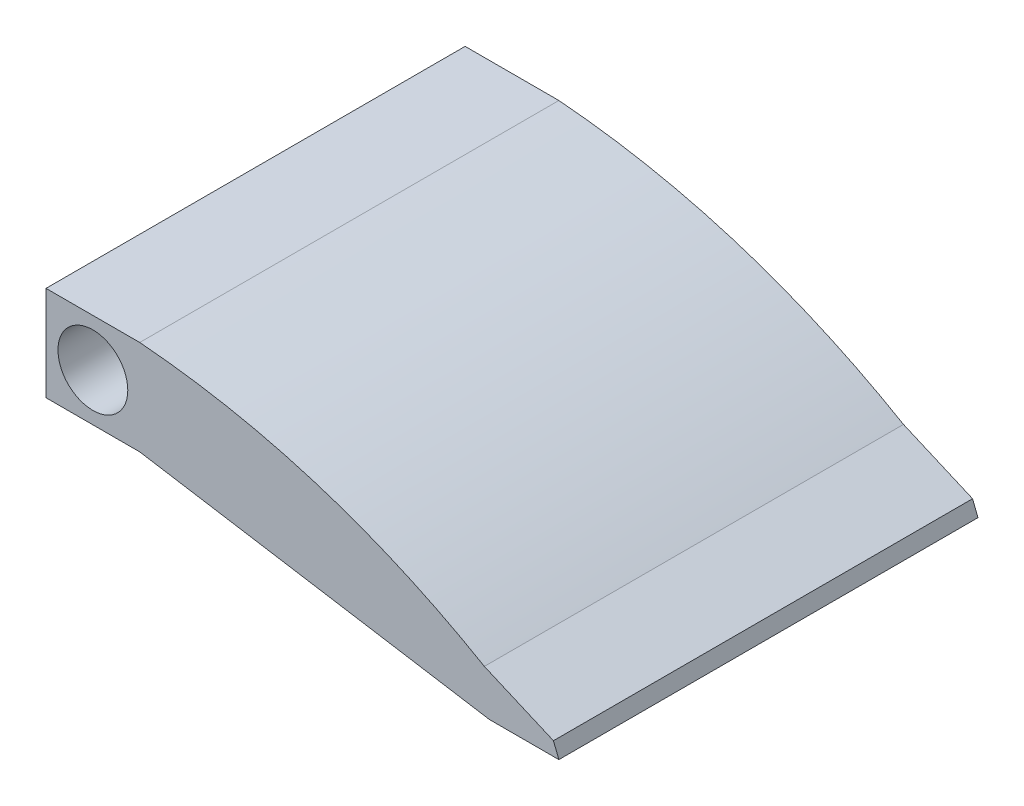
SolidWorks part; units mm, degrees
ref_plane "Front Plane" through (0, 0, 0) normal (0, 0, 1) x (1, 0, 0)
ref_plane "Top Plane" through (0, 0, 0) normal (0, 1, 0) x (1, 0, 0)
ref_plane "Right Plane" through (0, 0, 0) normal (1, 0, 0) x (0, 0, -1)
sketch "Sketch1" plane through (0, 0, 0) normal (0, 0, 1) x (1, 0, 0)
  line L1 (28.5002, -7.5) -> (33.5002, -7.5)
  line L2 (3.3698, -3.4063) -> (-3.3698, -3.4063)
  line L3 (3.3698, -3.4063) -> (3.3698, 3.4063)
  line L4 (3.3698, 3.4063) -> (-3.3698, 3.4063)
  line L5 (-3.3698, -3.4063) -> (-3.3698, 3.4063)
  line L6 (3.3698, -3.4063) -> (-3.3698, 3.4063) construction
  line L7 (3.3698, 3.4063) -> (-3.3698, -3.4063) construction
  line L8 (33.5002, -7.5) -> (33.1096, -6.5167)
  line L9 (33.1096, -6.5167) -> (28.1434, -4.3739)
  circle A0 centre (0, 0) radius 2.51
  spline S0 degree 2 poles (28.1434, -4.3739) (16.6661, 2.3165) (3.3698, 3.4063) knots 0 0 0 1 1 1
  spline S1 degree 1 poles (28.5002, -7.5) (3.3698, -3.4063) knots 0 0 1 1
extrude "Boss-Extrude1" add sketch "Sketch1" along normal blind 30.13 contours L5 L2 L3 L4 A0 | S1 L1 L8 L9 S0 L3
